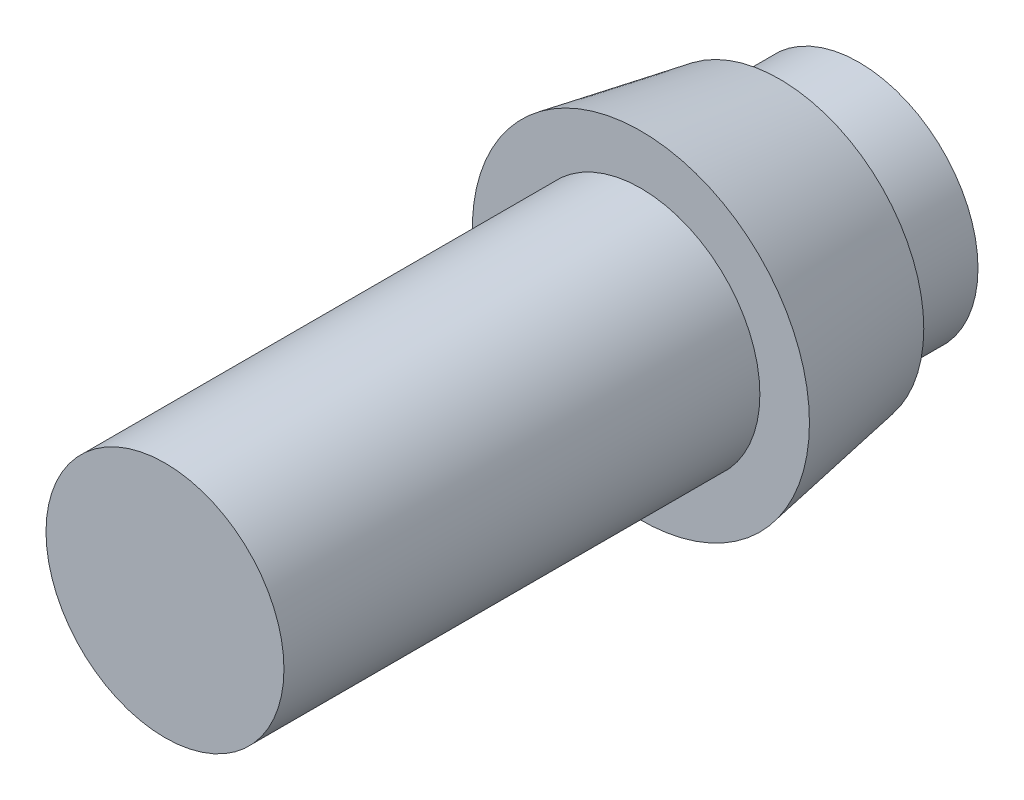
SolidWorks part; units mm, degrees
ref_plane "Front Plane" through (0, 0, 0) normal (0, 0, 1) x (1, 0, 0)
ref_plane "Top Plane" through (0, 0, 0) normal (0, 1, 0) x (1, 0, 0)
ref_plane "Right Plane" through (0, 0, 0) normal (1, 0, 0) x (0, 0, -1)
sketch "Sketch1" plane through (0, 0, 0) normal (0, 0, 1) x (1, 0, 0)
  circle A0 centre (0, 0) radius 6
  dimension "D1" = 12
extrude "Boss-Extrude1" add sketch "Sketch1" along normal blind 24
sketch "Sketch2" plane through (0, 0, 0) normal (0, 0, 1) x (1, 0, 0)
  circle A0 centre (0, 0) radius 8.5
  dimension "D1" = 17
extrude "Boss-Extrude2" add sketch "Sketch2" against normal blind 7 draft 10
sketch "Sketch3" plane through (0, 0, 0) normal (0, 0, 1) x (1, 0, 0)
  circle A0 centre (0, 0) radius 6
  dimension "D1" = 12
extrude "Boss-Extrude3" add sketch "Sketch3" against normal blind 4 from surface at -7 starting at face at (7.2657, 0, -7)
